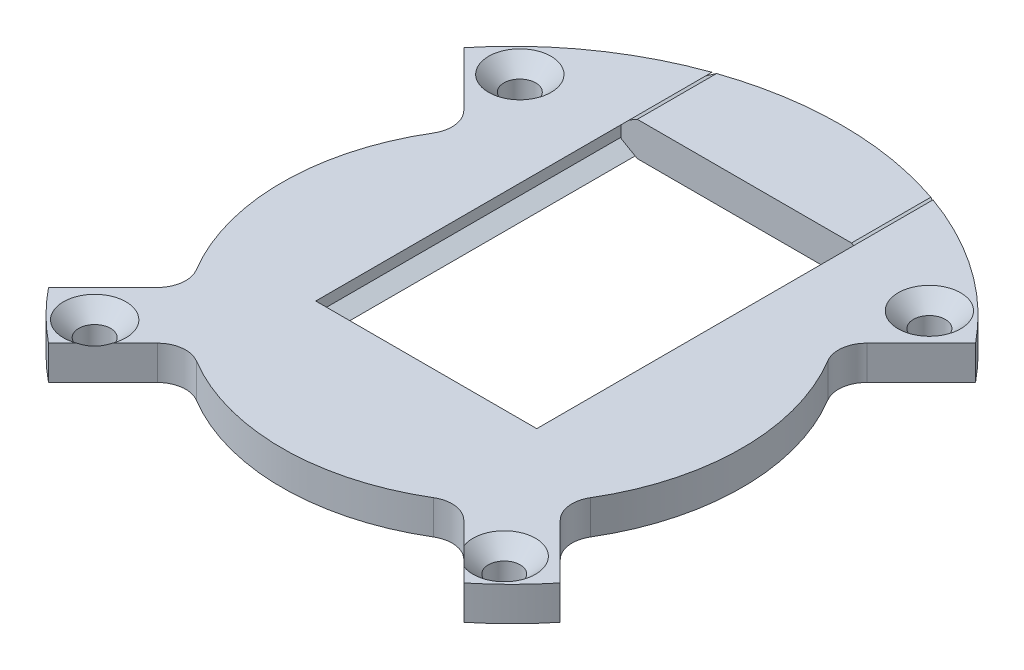
SolidWorks part; units mm, degrees
ref_plane "Front Plane" through (0, 0, 0) normal (0, 0, 1) x (1, 0, 0)
ref_plane "Top Plane" through (0, 0, 0) normal (0, 1, 0) x (1, 0, 0)
ref_plane "Right Plane" through (0, 0, 0) normal (1, 0, 0) x (0, 0, -1)
sketch "Sketch1" plane through (0, 0, 0) normal (0, 1, 0) x (1, 0, 0)
  circle A0 centre (0, 0) radius 29
  dimension "D1" = 58
extrude "Boss-Extrude1" add sketch "Sketch1" along normal mid plane 3
sketch "Sketch2" plane through (0, 1.5, 0) normal (0, 1, 0) x (1, 0, 0)
  line L0 (-11.025, 7.55) -> (-11.025, 29)
  line L1 (-11.025, -7.55) -> (11.025, -7.55)
  line L2 (-11.025, -7.55) -> (-11.025, 7.55)
  line L3 (-11.025, 7.55) -> (11.025, 7.55) construction
  line L4 (11.025, -7.55) -> (11.025, 7.55)
  line L5 (-11.025, -7.55) -> (11.025, 7.55) construction
  line L6 (-11.025, 7.55) -> (11.025, -7.55) construction
  line L7 (-11.025, 29) -> (11.025, 29)
  line L8 (11.025, 29) -> (11.025, 7.55)
  circle A0 centre (0, 0) radius 29 construction
  point P0 (0, 0)
  dimension "D1" = 7.55
  dimension "D2" = 22.05
extrude "Cut-Extrude1" cut sketch "Sketch2" against normal through all
sketch "Sketch3" plane through (0, 0, 7.55) normal (0, 0, -1) x (-1, 0, 0)
  line L0 (0, -1.5) -> (0, 1.5) construction
  line L1 (11.025, -1.5) -> (-11.025, -1.5) construction
  line L2 (11.025, 1.5) -> (-11.025, 1.5) construction
  line L3 (-11.525, -1.5) -> (-9.726, -1.5)
  line L5 (-9.726, -1.5) -> (-11.025, -0.75)
  line L6 (-11.025, -1.5) -> (-11.025, 1.5) construction
  line L7 (-11.025, -0.75) -> (-11.025, 0.75)
  line L8 (-11.025, 0.75) -> (-9.726, 1.5)
  line L9 (-9.726, 1.5) -> (-11.525, 1.5)
  line L10 (29, 1.5) -> (-29, 1.5) construction
  line L11 (-11.525, 1.5) -> (-11.525, -1.5)
  line L12 (-29, -1.5) -> (29, -1.5) construction
  line L13 (-11.025, -1.5) -> (-11.025, 1.5) construction
  line L21 (11.525, 1.5) -> (11.525, -1.5)
  line L22 (9.726, 1.5) -> (11.525, 1.5)
  line L23 (11.025, 0.75) -> (9.726, 1.5)
  line L24 (11.025, -0.75) -> (11.025, 0.75)
  line L25 (9.726, -1.5) -> (11.025, -0.75)
  line L26 (11.525, -1.5) -> (9.726, -1.5)
  point P10 (-11.025, 0)
  dimension "D1" = 0.5
  dimension "D2" = 60
  dimension "D3" = 1.5
extrude "Boss-Extrude2" add sketch "Sketch3" along normal up to surface (34.1615 mm away)
ref_plane "Plane1" through (0, 0, -20.45) normal (0, 0, -1) x (-1, 0, 0)
sketch "Sketch6" plane through (0, 0, -20.45) normal (0, 0, -1) x (-1, 0, 0)
  line L0 (-9.726, -1.5) -> (-11.025, -0.75) construction
  line L1 (-11.025, -0.75) -> (-11.025, 0.75) construction
  line L2 (-11.025, 0.75) -> (-9.726, 1.5) construction
  line L3 (-9.726, -1.5) -> (-11.025, -0.75) construction
  line L4 (-11.025, -0.75) -> (-11.025, 0.75) construction
  line L5 (-11.025, 0.75) -> (-9.726, 1.5) construction
  line L6 (-9.426, 1.5) -> (-10.875, 0.6634)
  line L7 (9.726, 1.5) -> (-9.726, 1.5) construction
  line L8 (-10.875, 0.6634) -> (-10.875, -0.6634)
  line L9 (-10.875, -0.6634) -> (-9.426, -1.5)
  line L10 (9.726, -1.5) -> (-9.726, -1.5) construction
  line L11 (0, 0) -> (0, 1.5) construction
  line L12 (10.875, -0.6634) -> (9.426, -1.5)
  line L13 (10.875, 0.6634) -> (10.875, -0.6634)
  line L14 (9.426, 1.5) -> (10.875, 0.6634)
  line L15 (-10.875, 0.6634) -> (-10.95, 0.7933) construction
  line L16 (-10.875, 0.6634) -> (-11.025, 0.6634) construction
  line L17 (10.875, -0.6634) -> (9.426, -1.5)
  line L18 (10.875, 0.6634) -> (10.875, -0.6634)
  line L19 (9.426, 1.5) -> (10.875, 0.6634)
  line L20 (-9.426, 1.5) -> (9.426, 1.5)
  line L21 (9.426, -1.5) -> (-9.426, -1.5)
  dimension "D1" = 0.15
extrude "Boss-Extrude3" add sketch "Sketch6" along normal up to surface (6.4337 mm away) separate body contours L21 L12 L13 L14 L20 L6 L8 L9
chamfer "Chamfer1" [suppressed] distance 2 angle 45
chamfer "Chamfer2" [suppressed] distance 2 angle 45
sketch "Sketch5" plane through (0, 1.5, 0) normal (0, 1, 0) x (1, 0, 0)
  circle A0 centre (0, 0) radius 25 construction
  circle A1 centre (0, 25) radius 1.4
  circle A2 centre (17.6777, 17.6777) radius 1.4
  circle A3 centre (25, 0) radius 1.4
  circle A4 centre (17.6777, -17.6777) radius 1.4
  circle A5 centre (0, -25) radius 1.4
  circle A6 centre (-17.6777, -17.6777) radius 1.4
  circle A7 centre (-25, 0) radius 1.4
  circle A8 centre (-17.6777, 17.6777) radius 1.4
  point P21 (0, 0)
  dimension "D1" = 50
  dimension "D2" = 2.8
  dimension "D3" = 8
extrude "Cut-Extrude2" [suppressed] cut sketch "Sketch5" against normal through all
hole_wizard "CSK for M2.5 Flat Head Machine Screw1" [suppressed] positions "Sketch7" profile "Sketch8" countersink size "M2.5" standard "ANSI Metric"
sketch "Sketch7" [suppressed] plane through (0, 1.5, 0) normal (0, 1, 0) x (1, 0, 0)
  circle A1 centre (0, -24) radius 1.4 construction
  circle A2 centre (0, 24) radius 1.4 construction
  circle A3 centre (24, 0) radius 1.4 construction
  point P13 (0, 24)
  point P16 (24, 0)
  point P19 (0, -24)
  point P22 (-24, 0)
sketch "Sketch8" plane through (0, 1.5, -24) normal (1, 0, 0) x (0, 0, 1)
  line L0 (0, 0) -> (0, 3)
  line L1 (0, 3) -> (1.35, 3)
  line L2 (1.35, 3) -> (1.35, 1.4)
  line L3 (1.35, 1.4) -> (2.75, 0)
  line L5 (2.75, 0) -> (0, 0)
  line L6 (-1.35, 1.4) -> (-2.75, 0) construction
  line L11 (0, -6.35) -> (0, 107.95) construction
  dimension "Thru Hole Dia." = 2.7
  dimension "Thru Hole Depth" = 3
  dimension "Near C'Sink Dia." = 5.5
  dimension "Near C'Sink Angle" = 90
sketch "Sketch10" [suppressed] plane through (0, 1.5, 0) normal (0, 1, 0) x (1, 0, 0)
  line L0 (0, 0) -> (0, -30) construction
  line L1 (15, -12.5) -> (11.5, -12.5) construction
  line L6 (-15, 12.5) -> (-11.5, 12.5) construction
  line L7 (-15, 12.5) -> (-15, -12.5) construction
  line L8 (-15, -12.5) -> (-11.5, -12.5) construction
  line L9 (-11.5, 12.5) -> (-11.5, -12.5) construction
  line L10 (-11.5, -12.5) -> (11.5, -12.5) construction
  line L11 (-11.5, -12.5) -> (-11.5, -9) construction
  line L12 (-11.5, -9) -> (11.5, -9) construction
  line L13 (11.5, -12.5) -> (11.5, -9) construction
  line L14 (11.5, 12.5) -> (11.5, -12.5) construction
  line L15 (15, 12.5) -> (11.5, 12.5) construction
  line L16 (15, 12.5) -> (15, -12.5) construction
  line L17 (0, 0) -> (-11.5, 0) construction
  line L18 (-11.5, -9) -> (-11.5, 12.5)
  line L19 (-11.5, 12.5) -> (-15, 12.5)
  line L20 (-15, 12.5) -> (-15, -12.5)
  line L21 (-15, -12.5) -> (15, -12.5)
  line L22 (15, -12.5) -> (15, 12.5)
  line L23 (15, 12.5) -> (11.5, 12.5)
  line L24 (11.5, 12.5) -> (11.5, -9)
  line L25 (11.5, -9) -> (-11.5, -9)
  arc A0 (-11.025, 27.9007) -> (11.025, 27.9007) centre (0, 0) ccw construction
  point P18 (-11.5, 0)
  point P36 (0, -12.5)
  point P37 (0, -9)
  dimension "D5" = 30
  dimension "D1" = 3.5
  dimension "D2" = 3.5
  dimension "D3" = 23
  dimension "D4" = 25
  dimension "D6" = 25
extrude "Boss-Extrude4" [suppressed] add sketch "Sketch10" along normal blind 5
sketch "Sketch11" [suppressed] plane through (0, 0, 9) normal (0, 0, -1) x (-1, 0, 0)
  line L0 (-11.5, 6.5) -> (11.5, 6.5) construction
  line L1 (0, 6.5) -> (-2.45, 5.0855) construction
  line L2 (-2.45, 5.0855) -> (-2.45, 2.2565)
  line L3 (-2.45, 2.2565) -> (0, 0.842)
  line L4 (0, 0.842) -> (2.45, 2.2565)
  line L5 (2.45, 2.2565) -> (2.45, 5.0855)
  line L6 (2.45, 5.0855) -> (0, 6.5) construction
  line L7 (-2.45, 5.0855) -> (-2.45, 6.5)
  line L8 (-2.45, 6.5) -> (2.45, 6.5)
  line L9 (2.45, 6.5) -> (2.45, 5.0855)
  circle A0 centre (0, 3.671) radius 2.45 construction
  dimension "D1" = 4.9
extrude "Cut-Extrude3" [suppressed] cut sketch "Sketch11" against normal blind 2
chamfer "Chamfer3" [suppressed] distance 3.5 angle 45
sketch "Sketch12" [suppressed] plane through (-11.5, 0, 0) normal (1, 0, 0) x (0, 0, -1)
  line L0 (0, 0) -> (0, 6.5) construction
  line L1 (-9, 6.5) -> (9, 6.5) construction
  line L2 (-9, 5.0855) -> (-9, 6.5)
  line L3 (-6.55, 6.5) -> (-9, 5.0855) construction
  line L4 (-9, 5.0855) -> (-9, 2.2565)
  line L5 (-9, 2.2565) -> (-6.55, 0.842)
  line L6 (-6.55, 0.842) -> (-4.1, 2.2565)
  line L7 (-4.1, 2.2565) -> (-4.1, 5.0855)
  line L8 (-4.1, 5.0855) -> (-6.55, 6.5) construction
  line L9 (-9, 6.5) -> (-4.1, 6.5)
  line L10 (-4.1, 6.5) -> (-4.1, 5.0855)
  line L11 (9, 6.5) -> (4.1, 6.5)
  line L12 (9, 5.0855) -> (9, 6.5)
  line L13 (9, 5.0855) -> (9, 2.2565)
  line L14 (9, 2.2565) -> (6.55, 0.842)
  line L15 (6.55, 0.842) -> (4.1, 2.2565)
  line L16 (4.1, 2.2565) -> (4.1, 5.0855)
  line L17 (4.1, 6.5) -> (4.1, 5.0855)
  line L18 (-9, 6.5) -> (-9, 1.5) construction
  circle A0 centre (-6.55, 3.671) radius 2.45 construction
  dimension "D2" = 4.9
extrude "Cut-Extrude4" [suppressed] cut sketch "Sketch12" against normal blind 2
mirror "Mirror1" [suppressed] about plane through (0, 0, 0) normal (1, 0, 0)
sketch "Sketch13" [suppressed] plane through (0, 0, 11) normal (0, 0, -1) x (-1, 0, 0)
  circle A0 centre (0, 3.671) radius 1.4
  dimension "D1" = 2.8
extrude "Cut-Extrude5" [suppressed] cut sketch "Sketch13" against normal blind 2
sketch "Sketch14" [suppressed] plane through (-15, 0, 0) normal (-1, 0, 0) x (0, 0, 1)
  line L0 (0, 6.5) -> (0, 0) construction
  line L1 (-9, 6.5) -> (9, 6.5) construction
  circle A0 centre (6.55, 3.671) radius 1.4
  circle A1 centre (-6.55, 3.671) radius 1.4
  dimension "D1" = 2.8
extrude "Cut-Extrude6" [suppressed] cut sketch "Sketch14" against normal through all both and the other way through all
sketch "Sketch15" [suppressed] plane through (0, 0, 0) normal (0, 1, 0) x (1, 0, 0)
  line L0 (0, 0) -> (-20.5061, 20.5061) construction
  line L1 (0, 0) -> (0, -29) construction
  arc A0 (-11.025, 26.8226) -> (11.025, 26.8226) centre (0, 0) ccw construction
  circle A1 centre (-21.2132, 21.2132) radius 1.5
  circle A2 centre (21.2132, 21.2132) radius 1.5
  circle A3 centre (21.2132, -21.2132) radius 1.5
  circle A4 centre (-21.2132, -21.2132) radius 1.5
  point P17 (0, 0)
  dimension "D2" = 3
  dimension "D1" = 135
  dimension "D3" = 1
  dimension "D4" = 4
extrude "Cut-Extrude7" [suppressed] cut sketch "Sketch15" against normal through all
sketch "Sketch16" plane through (0, 1.5, 0) normal (0, 1, 0) x (1, 0, 0)
  circle A0 centre (-18.0215, 18.707) radius 1.125 construction
  circle A1 centre (18.0215, 18.707) radius 1.125 construction
  circle A2 centre (18.0215, -18.707) radius 1.125 construction
  circle A3 centre (-18.0215, -18.707) radius 1.125 construction
  circle A4 centre (-18.0215, 18.707) radius 1.125
  circle A5 centre (18.0215, 18.707) radius 1.125
  circle A6 centre (18.0215, -18.707) radius 1.125
  circle A7 centre (-18.0215, -18.707) radius 1.125
sketch "Sketch17" plane through (0, 1.5, 0) normal (0, 1, 0) x (1, 0, 0)
  line L0 (22.5174, -18.2748) -> (17.7308, -13.4882)
  line L1 (20.5962, -16.3535) -> (17.7308, -13.4882) construction
  line L2 (13.4882, -17.7308) -> (18.2748, -22.5174)
  line L3 (0, 0) -> (48.6823, 0) construction
  line L4 (22.5174, 18.2748) -> (17.7308, 13.4882)
  line L5 (0, 0) -> (0, -42.5326) construction
  line L6 (-13.4882, -17.7308) -> (-18.2748, -22.5174)
  line L7 (-22.5174, 18.2748) -> (-17.7308, 13.4882)
  line L8 (-22.5174, -18.2748) -> (-17.7308, -13.4882)
  arc A0 (-9.726, 27.3204) -> (9.726, 27.3204) centre (0, 0) ccw construction
  arc A1 (17.7308, 13.4882) -> (17.3559, 10.4324) centre (19.4986, 11.7204) ccw construction
  arc A2 (17.3559, -10.4324) -> (17.7308, -13.4882) centre (19.4986, -11.7204) ccw construction
  arc A3 (17.7308, 13.4882) -> (17.3559, 10.4324) centre (19.4986, 11.7204) ccw
  arc A4 (17.3559, -10.4324) -> (17.7308, -13.4882) centre (19.4986, -11.7204) ccw
  arc A5 (-10.4324, -17.3559) -> (-13.4882, -17.7308) centre (-11.7204, -19.4986) ccw construction
  arc A6 (13.4882, -17.7308) -> (10.4324, -17.3559) centre (11.7204, -19.4986) ccw construction
  arc A7 (-10.4324, -17.3559) -> (-13.4882, -17.7308) centre (-11.7204, -19.4986) ccw
  arc A8 (13.4882, -17.7308) -> (10.4324, -17.3559) centre (11.7204, -19.4986) ccw
  arc A9 (-17.3559, 10.4324) -> (-17.7308, 13.4882) centre (-19.4986, 11.7204) ccw construction
  arc A10 (-17.7308, -13.4882) -> (-17.3559, -10.4324) centre (-19.4986, -11.7204) ccw construction
  arc A11 (-17.3559, 10.4324) -> (-17.7308, 13.4882) centre (-19.4986, 11.7204) ccw
  arc A12 (-17.7308, -13.4882) -> (-17.3559, -10.4324) centre (-19.4986, -11.7204) ccw
  arc A13 (17.3559, 10.4324) -> (17.3559, -10.4324) centre (0, 0) cw
  arc A14 (22.5174, 18.2748) -> (22.5174, -18.2748) centre (0, 0) cw
  arc A15 (-10.4324, -17.3559) -> (10.4324, -17.3559) centre (0, 0) ccw
  arc A16 (-17.7308, 13.4882) -> (-17.3559, 10.4324) centre (-19.4986, 11.7204) cw
  arc A17 (-17.3559, 10.4324) -> (-17.3559, -10.4324) centre (0, 0) ccw
  arc A18 (-17.3559, -10.4324) -> (-17.7308, -13.4882) centre (-19.4986, -11.7204) cw
  arc A19 (-22.5174, 18.2748) -> (-22.5174, -18.2748) centre (0, 0) ccw
  arc A20 (-18.2748, -22.5174) -> (18.2748, -22.5174) centre (0, 0) ccw
  arc M4 (-9.726, 27.3204) -> (9.726, 27.3204) centre (0, 0) ccw
extrude "Cut-Extrude8" cut sketch "Sketch17" against normal through all contours A17 A11 L7 L8 A12 M4 | A15 A7 L6 L2 A8 M4 | A3 A13 A4 L0 L4 M4
hole_wizard "CSK for M2.5 Flat Head Machine Screw2" positions "Sketch18" profile "Sketch19" countersink size "M2.5" standard "ANSI Metric" end condition through all
sketch "Sketch18" plane through (0, 1.5, 0) normal (0, 1, 0) x (1, 0, 0)
  point P0 (-18.0215, 18.707)
  point P3 (18.0215, 18.707)
  point P6 (18.0215, -18.707)
  point P9 (-18.0215, -18.707)
sketch "Sketch19" plane through (-18.0215, 1.5, -18.707) normal (1, 0, 0) x (0, 0, 1)
  line L0 (0, 0) -> (0, 3)
  line L1 (0, 3) -> (1.4, 3)
  line L2 (1.4, 3) -> (1.4, 1.35)
  line L3 (1.4, 1.35) -> (2.75, 0)
  line L5 (2.75, 0) -> (0, 0)
  line L6 (-1.4, 1.35) -> (-2.75, 0) construction
  line L11 (0, -6.35) -> (0, 107.95) construction
  dimension "Thru Hole Dia." = 2.8
  dimension "Thru Hole Depth" = 3
  dimension "Near C'Sink Dia." = 5.5
  dimension "Near C'Sink Angle" = 90
equation "\"m2.5 width\"= 4.9mm"
equation "\"D1@Sketch11\"=\"m2.5 width\""
equation "\"D2@Sketch12\"=\"m2.5 width\""
